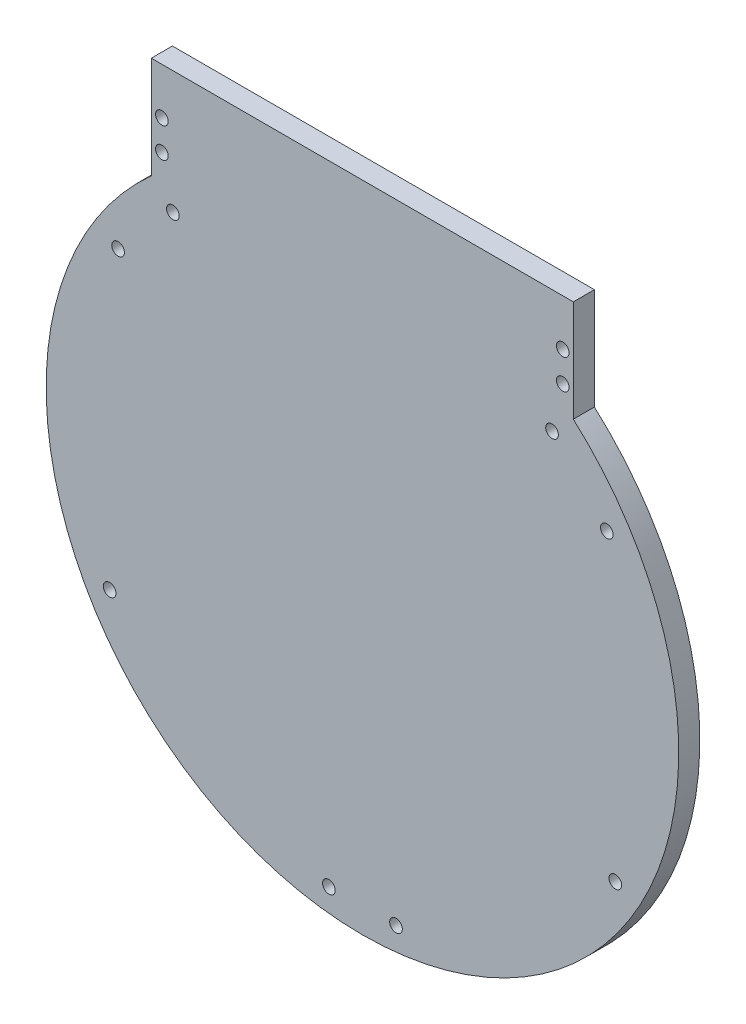
SolidWorks part; units mm, degrees
material "Acrílico (médio-alto impacto)"
ref_plane "Plano frontal" through (0, 0, 0) normal (0, 0, 1) x (1, 0, 0)
ref_plane "Plano superior" through (0, 0, 0) normal (0, 1, 0) x (1, 0, 0)
ref_plane "Plano direito" through (0, 0, 0) normal (1, 0, 0) x (0, 0, -1)
sketch "Esboço1" plane through (0, 0, 0) normal (0, 0, 1) x (1, 0, 0)
  line L0 (44.4954, -168.4305) -> (22.4463, -168.4305) construction
  line L1 (-33.4554, -168.4305) -> (-55.5046, -168.4305) construction
  line L2 (44.4954, -168.4305) -> (44.4954, -144.3322)
  line L3 (-55.5734, -168.3931) -> (-55.5734, -144.3322)
  line L4 (-55.5734, -144.3322) -> (44.4954, -144.3322)
  line L10 (-55.5046, -168.4305) -> (-55.5734, -168.3931)
  arc A0 (-55.5046, -168.4305) -> (44.4954, -168.4305) centre (-5.5046, -224.3322) ccw
  arc A1 (-33.4554, -168.4305) -> (22.4463, -168.4305) centre (-5.5046, -224.3322) ccw construction
  dimension "D1" = 150
  dimension "D2" = 125
  dimension "D3" = 80
extrude "Ressalto-extrusão1" add sketch "Esboço1" along normal blind 5 contours A0 L2 L4 L3 L10
sketch "Esboço2" plane through (0, 0, 5) normal (0, 0, 1) x (1, 0, 0)
  line L1 (-5.5046, -299.3322) -> (-5.5046, -271.3491) construction
  circle A0 centre (39.4463, -173.4305) radius 1.5
  circle A1 centre (52.4463, -187.4305) radius 1.5
  circle A2 centre (54.4463, -258.4305) radius 1.5
  circle A3 centre (-13.4554, -293.4305) radius 1.5
  circle A4 centre (2.4463, -293.4305) radius 1.5
  circle A5 centre (-65.4554, -258.4305) radius 1.5
  circle A8 centre (-63.4554, -187.4305) radius 1.5
  circle A9 centre (-50.4554, -173.4305) radius 1.5
  dimension "D3" = 3
  dimension "D6" = 3
  dimension "D9" = 3
  dimension "D12" = 3
extrude "Corte-extrusão1" cut sketch "Esboço2" against normal blind 10
sketch "Esboço3" plane through (0, 0, 5) normal (0, 0, 1) x (1, 0, 0)
  line L0 (-55.5734, -144.3322) -> (44.4954, -144.3322) construction
  line L1 (-55.5734, -168.3931) -> (-55.5734, -144.3322) construction
  line L2 (44.4954, -168.4305) -> (44.4954, -144.3322) construction
  circle A0 centre (-53.0734, -162.4305) radius 1.5
  circle A1 centre (-53.0734, -155.3322) radius 1.5
  circle A2 centre (41.9954, -162.4305) radius 1.5
  circle A3 centre (41.9954, -155.3322) radius 1.5
  dimension "D1" = 11
  dimension "D2" = 6
  dimension "D3" = 2.5
  dimension "D4" = 2.5
  dimension "D5" = 3
  dimension "D6" = 3
  dimension "D7" = 11
  dimension "D8" = 6
  dimension "D9" = 2.5
  dimension "D10" = 2.5
  dimension "D11" = 3
  dimension "D12" = 3
extrude "Corte-extrusão2" cut sketch "Esboço3" against normal through all
